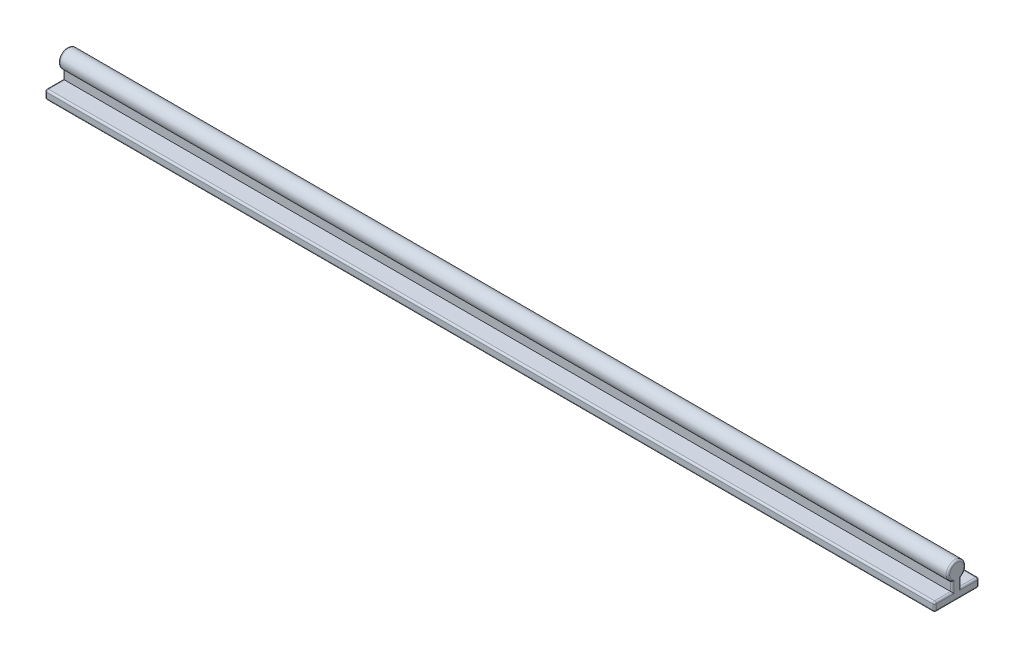
SolidWorks part; units mm, degrees
material "1.5714 (16NiCr4)"
ref_plane "前视基准面" through (0, 0, 0) normal (0, 0, 1) x (1, 0, 0)
ref_plane "上视基准面" through (0, 0, 0) normal (0, 1, 0) x (1, 0, 0)
ref_plane "右视基准面" through (0, 0, 0) normal (1, 0, 0) x (0, 0, -1)
sketch "Sketch2" plane through (0, 0, 0) normal (1, 0, 0) x (0, 0, -1)
  line L0 (0, 90.3237) -> (0, -90.3237) construction
  line L1 (25, 0) -> (-25, 0)
  line L2 (-25, 0) -> (-25, 10)
  line L3 (-25, 10) -> (-5, 10)
  line L4 (-5, 10) -> (-5, 20)
  line L5 (25, 0) -> (25, 10)
  line L6 (25, 10) -> (5, 10)
  line L7 (5, 10) -> (5, 20)
  arc A0 (5, 20) -> (-5, 20) centre (0, 28.6603) ccw
  point P9 (0, 78.8973)
  point P12 (0, 0)
  dimension "D4" = 10
  dimension "D1" = 25
  dimension "D2" = 10
  dimension "D3" = 5
  dimension "D5" = 10
extrude "Boss-Extrude1" add sketch "Sketch2" along normal mid plane 1000
fillet "Fillet1" radius 2 20 edges at (0, 10, 25) (0, 0, 25) (0, 0, -25) (0, 10, -25) (500, 5, -25) (500, 0, 0) (500, 5, 25) (500, 10, 15) (500, 15, 5) (500, 38.6603, 0) (500, 15, -5) (500, 10, -15) (-500, 15, -5) (-500, 38.6603, 0) (-500, 15, 5) (-500, 10, 15) (-500, 5, 25) (-500, 0, 0) (-500, 5, -25) (-500, 10, -15)
